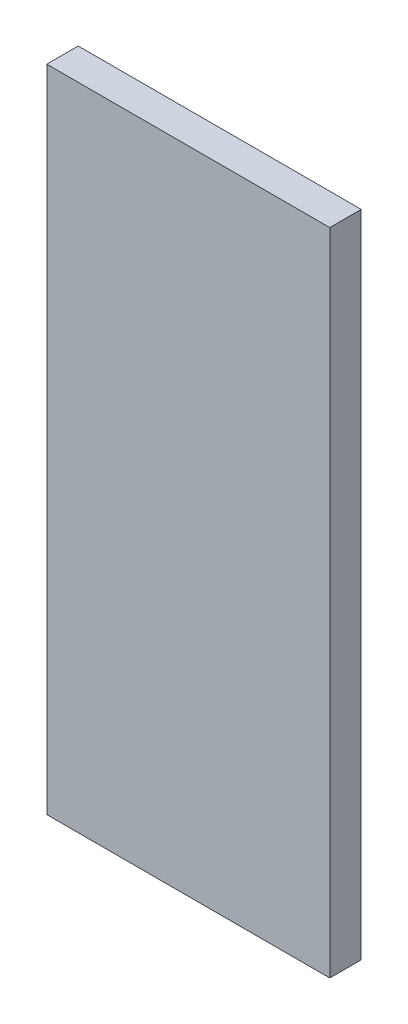
SolidWorks part; units mm, degrees
ref_plane "Plan de face" through (0, 0, 0) normal (0, 0, 1) x (1, 0, 0)
ref_plane "Plan de dessus" through (0, 0, 0) normal (0, 1, 0) x (1, 0, 0)
ref_plane "Plan de droite" through (0, 0, 0) normal (1, 0, 0) x (0, 0, -1)
sketch "Esquisse1" plane through (0, 0, 0) normal (0, 0, 1) x (1, 0, 0)
  line L1 (-13.5, 31) -> (13.5, 31)
  line L2 (-13.5, 31) -> (-13.5, -31)
  line L3 (-13.5, -31) -> (13.5, -31)
  line L4 (13.5, 31) -> (13.5, -31)
  line L5 (-13.5, 31) -> (13.5, -31) construction
  line L6 (-13.5, -31) -> (13.5, 31) construction
  point P0 (0, 0)
  dimension "D1" = 27
  dimension "D2" = 62
extrude "Boss.-Extru.1" add sketch "Esquisse1" along normal blind 3
